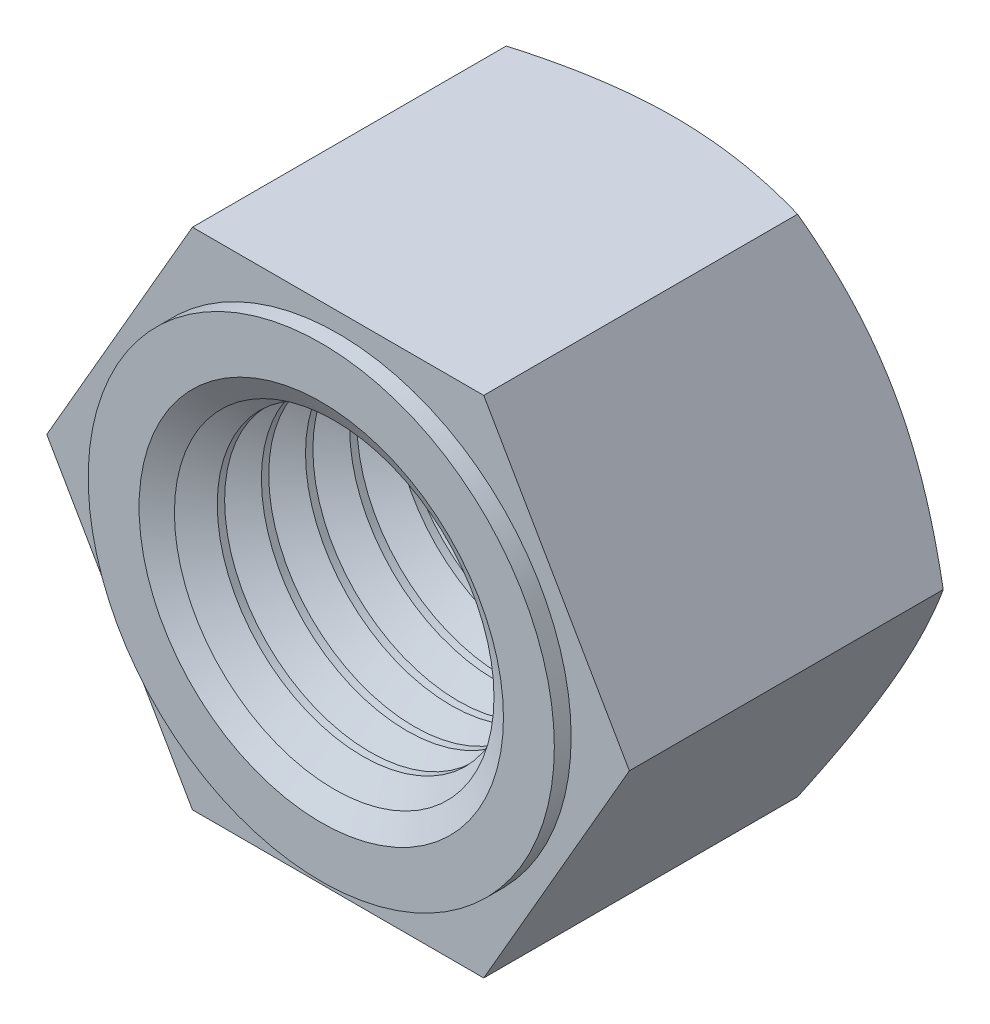
SolidWorks part; units mm, degrees
ref_plane "Front" through (0, 0, 0) normal (0, 0, 1) x (1, 0, 0)
ref_plane "Top" through (0, 0, 0) normal (0, 1, 0) x (1, 0, 0)
ref_plane "Right" through (0, 0, 0) normal (1, 0, 0) x (0, 0, -1)
sketch "Sketch1" plane through (0, 0, 0) normal (0, 0, 1) x (1, 0, 0)
  line L1 (5.1962, -9) -> (10.3923, 0)
  line L2 (10.3923, 0) -> (5.1962, 9)
  line L3 (5.1962, 9) -> (-5.1962, 9)
  line L4 (-5.1962, 9) -> (-10.3923, 0)
  line L5 (-10.3923, 0) -> (-5.1962, -9)
  line L6 (-5.1962, -9) -> (5.1962, -9)
  circle A0 centre (0, 0) radius 9 construction
  circle A1 centre (0, 0) radius 5.188
  dimension "D1" = 10.376
  dimension "s" = 18
extrude "BaseNut" add sketch "Sketch1" against normal blind 12
cosmetic thread "ThreadCosmetic1" [suppressed] parameters "D2"=13
sketch "Sketch2" plane through (-16.7061, 0, -15.0481) normal (0, 1, 0) x (0, 0, 1)
  line L0 (-23.7227, 16.7061) -> (22.0646, 16.7061) construction
  line L2 (3.0481, 25.7061) -> (3.0481, 27.0985)
  line L4 (3.0481, 27.0985) -> (3.852, 27.0985)
  line L6 (3.852, 27.0985) -> (3.0481, 25.7061)
  dimension "D1" = 30
  dimension "S1" = 18
revolve "Chamfer1" cut sketch "Sketch2" angle 360 about L0
sketch "Sketch6" plane through (-9.1975, 0, -10.2525) normal (0, 1, 0) x (0, 0, 1)
  line L0 (23.3574, 9.1975) -> (-22.3023, 9.1975) construction
  line L2 (-1.7475, 14.3855) -> (-1.7475, 15.6975)
  line L4 (-1.7475, 15.6975) -> (-0.99, 14.3855)
  line L6 (-0.99, 14.3855) -> (-1.7475, 14.3855)
  dimension "da" = 13
  dimension "D2" = 60
revolve "EndChamfer1" cut sketch "Sketch6" angle 360 about L0
sketch "Sketch5" plane through (-14.793, 0, -16.9612) normal (0, 1, 0) x (0, 0, 1)
  line L0 (-22.5748, 14.793) -> (24.743, 14.793) construction
  line L2 (16.9612, 23.108) -> (16.9612, 25.1853)
  line L4 (16.9612, 25.1853) -> (15.7619, 25.1853)
  line L6 (15.7619, 25.1853) -> (16.9612, 23.108)
  dimension "dw1" = 16.63
  dimension "D2" = 30
revolve "Chamfer2" [suppressed] cut sketch "Sketch5" angle 360 about L0
sketch "Sketch3" plane through (-18.4892, 11.179, 0) normal (0, 0, 1) x (1, 0, 0)
  circle A1 centre (18.4892, -11.179) radius 5.188 construction
  circle A2 centre (18.4892, -11.179) radius 8.315
  circle A3 centre (18.4892, -11.179) radius 5.188
  dimension "dw" = 16.63
extrude "Extrude1" add sketch "Sketch3" along normal blind 0.6
chamfer "EndChamfer3" distance 1.312 angle 30 1 edges at (5.188, 0, 0.6)
chamfer "EndChamfer2" [suppressed] distance 0.4 angle 45
sketch "Sketch7" plane through (0, 0, 0) normal (0, 1, 0) x (1, 0, 0)
  line L0 (0, 61.6098) -> (0, -22.305) construction
  line L1 (3.876, 11.8985) -> (5.188, 11.8985)
  line L2 (5.188, 11.8985) -> (6.3242, 11.2425)
  line L3 (6.3242, 11.2425) -> (5.188, 10.5865)
  line L4 (5.188, 10.5865) -> (3.876, 10.5865)
  line L5 (3.876, 10.5865) -> (3.876, 11.8985)
  line L6 (5.188, 11.2425) -> (-5.188, 11.2425) construction
  dimension "D1" = 1.312
  dimension "D2" = 10.376
revolve "Cut-Revolve10" cut sketch "Sketch7" angle 360 about L0
pattern_linear "LPattern10" count 8 spacing 1.5744 along (0, 0, 1) of "Cut-Revolve10"
equation "\"D1@EndChamfer3\" = ( \"da@Sketch6\" - \"D1@Sketch1\" )  / 2"
equation "\"D1@EndChamfer2\" = \"m@BaseNut\" / 30"
equation "\"S1@Sketch2\" = \"s@Sketch1\""
equation "\"D2@Sketch7\" = \"D1@Sketch1\""
equation "\"D1@Sketch7\" = (  \"D2@ThreadCosmetic1\" - \"D1@Sketch1\" )  / 2"
equation "\"D3@LPattern10\" = \"D1@Sketch7\" * 1.2"
equation "\"D1@LPattern10\" =  \"m@BaseNut\"  / \"D3@LPattern10\""
